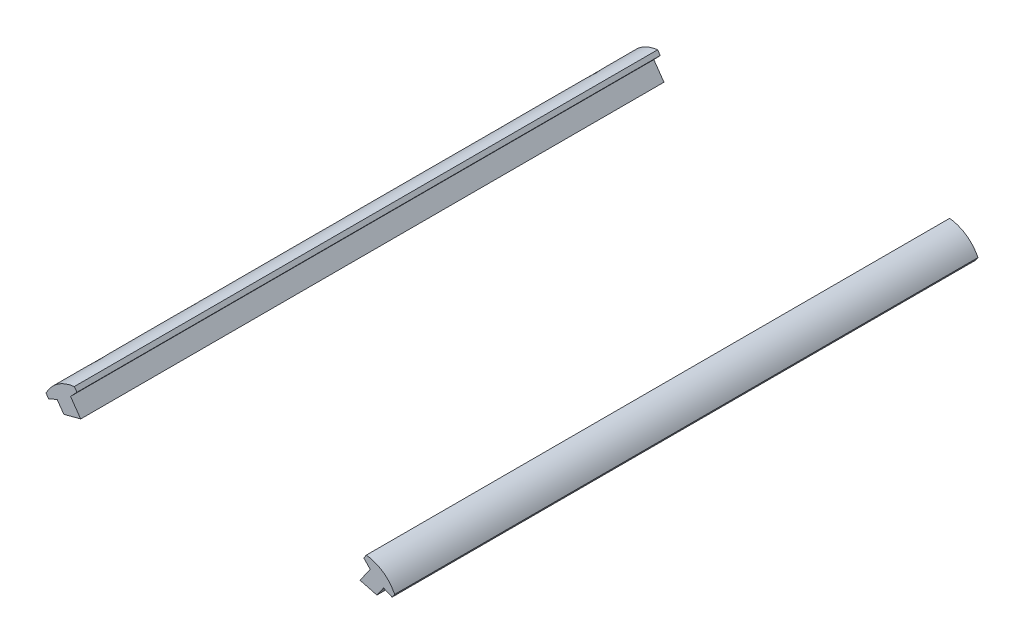
SolidWorks part; units mm, degrees
ref_plane "Front Plane" through (0, 0, 0) normal (0, 0, 1) x (1, 0, 0)
ref_plane "Top Plane" through (0, 0, 0) normal (0, 1, 0) x (1, 0, 0)
ref_plane "Right Plane" through (0, 0, 0) normal (1, 0, 0) x (0, 0, -1)
sketch "Sketch1" plane through (0, 0, 0) normal (0, 0, 1) x (1, 0, 0)
  line L0 (0, 0) -> (0, 152.4) construction
  line L1 (-59.9912, 144.0357) -> (-8.1938, 180.2969) construction
  line L3 (-6.373, 177.696) -> (-33.3007, 158.8449) construction
  line L4 (6.373, 177.696) -> (33.3007, 158.8449) construction
  line L5 (-33.3007, 158.8449) -> (-27.0899, 149.973) construction
  line L6 (33.3007, 158.8449) -> (27.0899, 149.973) construction
  line L7 (-36.4912, 147.9667) -> (-39.1424, 151.7538)
  line L8 (-46.5547, 158.6235) -> (-28.8566, 133.3425) construction
  line L9 (-39.1424, 151.7538) -> (-37.4676, 153.5263)
  line L10 (-34.2947, 155.7476) -> (-23.7131, 163.1553) construction
  line L13 (-40.8893, 146.8122) -> (-42.6364, 149.3078)
  line L14 (-42.6364, 149.3078) -> (-44.875, 148.3407)
  line L17 (-37.4676, 153.5263) -> (-38.145, 154.4939)
  line L18 (-44.875, 148.3407) -> (-45.5523, 149.3083)
  line L19 (36.4912, 147.9667) -> (39.1424, 151.7538)
  line L20 (40.8893, 146.8122) -> (42.6364, 149.3078)
  line L21 (44.875, 148.3407) -> (45.5523, 149.3083)
  line L22 (42.6364, 149.3078) -> (44.875, 148.3407)
  line L23 (39.1424, 151.7538) -> (37.4676, 153.5263)
  line L24 (37.4676, 153.5263) -> (38.145, 154.4939)
  line L27 (59.9912, 144.0357) -> (8.1938, 180.2969) construction
  arc A1 (6.373, 177.696) -> (-6.373, 177.696) centre (0, 168.5925) ccw construction
  arc A2 (8.1938, 180.2969) -> (-8.1938, 180.2969) centre (0, 168.5925) ccw construction
  circle A4 centre (0, 168.5925) radius 11.1125 construction
  arc A8 (62.4412, 139.0211) -> (40.8893, 146.8122) centre (0, 0) ccw construction
  arc A9 (36.4912, 147.9667) -> (27.0899, 149.973) centre (0, 0) ccw construction
  arc A10 (-40.8893, 146.8122) -> (-62.4412, 139.0211) centre (0, 0) ccw construction
  arc A11 (-27.0899, 149.973) -> (-36.4912, 147.9667) centre (0, 0) ccw construction
  arc A12 (40.8893, 146.8122) -> (36.4912, 147.9667) centre (0, 0) ccw
  arc A13 (-36.4912, 147.9667) -> (-40.8893, 146.8122) centre (0, 0) ccw
  spline S0 degree 2 poles (-45.5523, 149.3083) (-43.1806, 153.8037) (-38.145, 154.4939) knots 0 0 0 1 1 1
  spline S1 degree 2 poles (45.5523, 149.3083) (43.1806, 153.8037) (38.145, 154.4939) knots 0 0 0 1 1 1
  spline S2 degree 2 poles (-59.9912, 144.0357) (-62.7825, 142.084) (-62.4412, 139.0211) knots 0 0 0 1 1 1 construction
  spline S3 degree 2 poles (59.9912, 144.0357) (62.7825, 142.084) (62.4412, 139.0211) knots 0 0 0 1 1 1 construction
  dimension "D2" = 168.5925
  dimension "D3" = 22.225
  dimension "D4" = 28.575
  dimension "D13" = 1.1811
  dimension "D14" = 2.3424
  dimension "D15" = 1.791
  dimension "D16" = 3.2237
  dimension "D6" = 5.8922
  dimension "D17" = 304.8
  dimension "D5" = 10.8299
  dimension "D7" = 24.2562
  dimension "D8" = 43.8553
  dimension "D9" = 9.1452
  dimension "D10" = 3.0464
  dimension "D11" = 4.6229
  dimension "D12" = 2.4386
  dimension "D18" = 147.2577
extrude "Boss-Extrude1" add sketch "Sketch1" along normal blind 152.4
equation "\"diameter\"= 12in'diameter of rocket"
